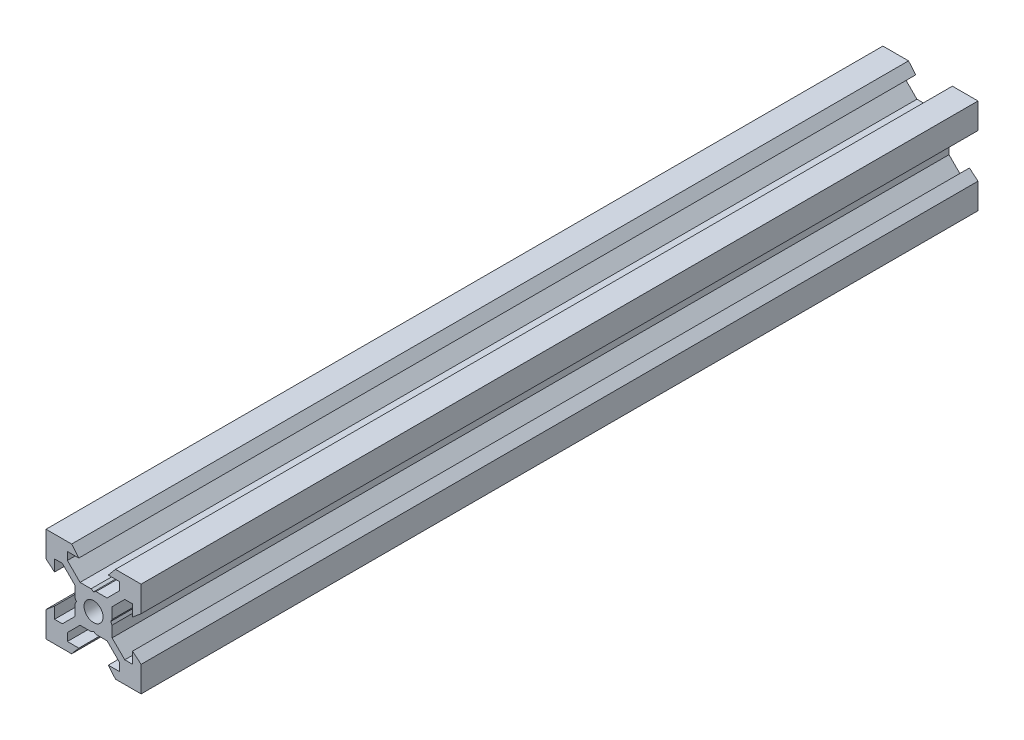
SolidWorks part; units mm, degrees
ref_plane "Front Plane" through (0, 0, 0) normal (0, 0, 1) x (1, 0, 0)
ref_plane "Top Plane" through (0, 0, 0) normal (0, 1, 0) x (1, 0, 0)
ref_plane "Right Plane" through (0, 0, 0) normal (1, 0, 0) x (0, 0, -1)
sketch "Sketch1" plane through (0, 0, 0) normal (0, 0, 1) x (1, 0, 0)
  line L0 (10, 10) -> (4.6104, 10) construction
  line L1 (10, 10) -> (10, 4.6104) construction
  line L2 (10, -10) -> (10, -4.6104) construction
  line L3 (10, -10) -> (4.6104, -10) construction
  line L4 (10, 10) -> (10, 4.6104)
  line L5 (6.5607, 5.5) -> (8.2, 5.5)
  line L6 (5.5, 8.2) -> (5.5, 6.5607)
  line L7 (10, 10) -> (4.6104, 10)
  line L8 (10, 10) -> (10, 4.6104)
  line L9 (6.5607, 5.5) -> (3.9, 2.8393)
  line L10 (5.5, 6.5607) -> (2.8393, 3.9)
  line L11 (10, 4.6104) -> (8.2, 3.1)
  line L12 (4.6104, 10) -> (3.1, 8.2)
  line L13 (8.2, 3.1) -> (8.2, 5.5)
  line L14 (3.1, 8.2) -> (5.5, 8.2)
  line L15 (-6.5607, 5.5) -> (-8.2, 5.5)
  line L16 (6.5607, -5.5) -> (8.2, -5.5)
  line L17 (3.1, -8.2) -> (5.5, -8.2)
  line L18 (8.2, -3.1) -> (8.2, -5.5)
  line L19 (4.6104, -10) -> (3.1, -8.2)
  line L20 (10, -4.6104) -> (8.2, -3.1)
  line L21 (0.5196, -3.9) -> (0, -3.6)
  line L22 (0.5196, 3.9) -> (0, 3.6)
  line L23 (3.6, 0) -> (3.9, -0.5196)
  line L24 (3.9, 0.5196) -> (3.6, 0)
  line L25 (3.9, 0.5196) -> (3.9, 2.8393)
  line L26 (2.8393, 3.9) -> (0.5196, 3.9)
  line L27 (3.9, -2.8393) -> (3.9, -0.5196)
  line L28 (2.8393, -3.9) -> (0.5196, -3.9)
  line L29 (5.5, -6.5607) -> (2.8393, -3.9)
  line L30 (6.5607, -5.5) -> (3.9, -2.8393)
  line L31 (10, -10) -> (10, -4.6104)
  line L32 (10, -10) -> (4.6104, -10)
  line L33 (5.5, -8.2) -> (5.5, -6.5607)
  line L34 (-6.5607, -5.5) -> (-8.2, -5.5)
  line L35 (10, -10) -> (10, -4.6104)
  line L36 (0, 0) -> (0, 8.2) construction
  line L37 (-10, -10) -> (-4.6104, -10) construction
  line L38 (-10, -10) -> (-10, -4.6104) construction
  line L39 (-10, 10) -> (-10, 4.6104) construction
  line L40 (-10, 10) -> (-4.6104, 10) construction
  line L41 (-10, -10) -> (-10, -4.6104)
  line L43 (-5.5, -8.2) -> (-5.5, -6.5607)
  line L44 (-10, -10) -> (-4.6104, -10)
  line L45 (-10, -10) -> (-10, -4.6104)
  line L46 (-6.5607, -5.5) -> (-3.9, -2.8393)
  line L47 (-5.5, -6.5607) -> (-2.8393, -3.9)
  line L48 (-2.8393, -3.9) -> (-0.5196, -3.9)
  line L49 (-3.9, -2.8393) -> (-3.9, -0.5196)
  line L50 (-2.8393, 3.9) -> (-0.5196, 3.9)
  line L51 (-3.9, 0.5196) -> (-3.9, 2.8393)
  line L52 (-3.9, 0.5196) -> (-3.6, 0)
  line L53 (-3.6, 0) -> (-3.9, -0.5196)
  line L54 (-0.5196, 3.9) -> (0, 3.6)
  line L55 (-0.5196, -3.9) -> (0, -3.6)
  line L56 (-10, -4.6104) -> (-8.2, -3.1)
  line L57 (-4.6104, -10) -> (-3.1, -8.2)
  line L58 (-8.2, -3.1) -> (-8.2, -5.5)
  line L59 (-3.1, -8.2) -> (-5.5, -8.2)
  line L60 (-10, -10) -> (10, -10) construction
  line L61 (-10, -10) -> (-10, 10) construction
  line L62 (-3.1, 8.2) -> (-5.5, 8.2)
  line L63 (-8.2, 3.1) -> (-8.2, 5.5)
  line L64 (-4.6104, 10) -> (-3.1, 8.2)
  line L65 (-10, 4.6104) -> (-8.2, 3.1)
  line L66 (-5.5, 6.5607) -> (-2.8393, 3.9)
  line L67 (-6.5607, 5.5) -> (-3.9, 2.8393)
  line L68 (-10, 10) -> (-10, 4.6104)
  line L69 (-10, 10) -> (-4.6104, 10)
  line L70 (-5.5, 8.2) -> (-5.5, 6.5607)
  line L71 (-10, 10) -> (10, 10) construction
  line L72 (-10, 10) -> (-10, 4.6104)
  line L73 (10, -10) -> (10, 10) construction
  line L74 (-10, -10) -> (10, 10) construction
  line L75 (-10, 10) -> (10, -10) construction
  circle A0 centre (0, 0) radius 2
  dimension "D7" = 4
  dimension "D1" = 20
  dimension "D2" = 5.3896
  dimension "D3" = 4.5
  dimension "D4" = 50
  dimension "D5" = 1.8
  dimension "D6" = 1.5104
  dimension "D8" = 5.5
  dimension "D9" = 120
  dimension "D10" = 0.3
  dimension "D11" = 2.3197
  dimension "D12" = 7.8
  dimension "D13" = 7.8
  dimension "D14" = 1.5
  dimension "D15" = 2.6607
extrude "Boss-Extrude1" add sketch "Sketch1" along normal mid plane 176 contours L70 L62 L64 L69 L68 L65 L63 L15 L67 L51 L52 L53 L49 L46 L34 L58 L56 L41 L44 L57 L59 L43 L47 L48 L55 L21 L28 L29 L33 L17 L19 L32 L31 L20 L18 L16 L30 L27 L23 L24 L25 L9 L5 L13 L11 L4 L7 L12 L14 L6 L10
